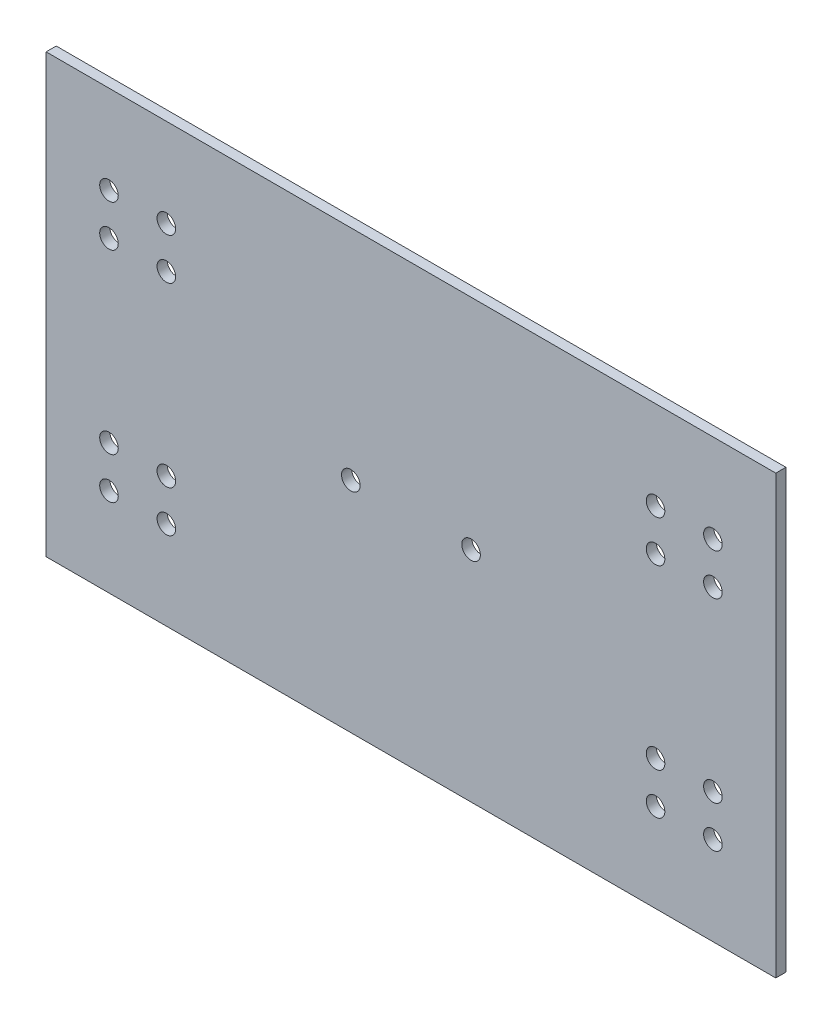
SolidWorks part; units mm, degrees
ref_plane "Alzado" through (0, 0, 0) normal (0, 0, 1) x (1, 0, 0)
ref_plane "Planta" through (0, 0, 0) normal (0, 1, 0) x (1, 0, 0)
ref_plane "Vista lateral" through (0, 0, 0) normal (1, 0, 0) x (0, 0, -1)
sketch "Sketch1" plane through (0, 0, 0) normal (0, 0, 1) x (1, 0, 0)
  line L0 (267, 160) -> (267, 0)
  line L1 (267, 160) -> (0, 160)
  line L2 (267, 0) -> (0, 0)
  line L3 (0, 160) -> (0, 0)
  line L4 (23, 51) -> (-40.3044, 51) construction
  line L5 (23, 29) -> (-41.338, 29) construction
  line L6 (47.4, 47.6) -> (47.4, 14.1246) construction
  line L7 (19.6, 47.6) -> (19.6, 13.494) construction
  line L8 (23, 47.6) -> (44, 32.4) construction
  line L9 (23, 32.4) -> (44, 47.6) construction
  line L10 (133.5, 40) -> (133.5, 23.6262) construction
  line L11 (267, 80) -> (183.2601, 80) construction
  line L12 (183.2601, 60) -> (104.6684, 60) construction
  circle A0 centre (6, 154) radius 3.4
  circle A1 centre (6, 6) radius 3.4
  circle A2 centre (261, 154) radius 3.4
  circle A3 centre (261, 6) radius 3.4
  circle A4 centre (111.5, 40) radius 3.4
  circle A5 centre (155.5, 40) radius 3.4
  circle A6 centre (23, 47.6) radius 3.4
  circle A7 centre (44, 47.6) radius 3.4
  circle A8 centre (23, 32.4) radius 3.4
  circle A9 centre (44, 32.4) radius 3.4
  circle A10 centre (223, 32.4) radius 3.4
  circle A11 centre (223, 47.6) radius 3.4
  circle A12 centre (244, 47.6) radius 3.4
  circle A13 centre (244, 32.4) radius 3.4
  circle A14 centre (23, 127.6) radius 3.4
  circle A15 centre (23, 112.4) radius 3.4
  circle A16 centre (44, 112.4) radius 3.4
  circle A17 centre (44, 127.6) radius 3.4
  circle A18 centre (223, 112.4) radius 3.4
  circle A19 centre (223, 127.6) radius 3.4
  circle A20 centre (244, 127.6) radius 3.4
  circle A21 centre (244, 112.4) radius 3.4
  circle A22 centre (111.5, 80) radius 3.4
  circle A23 centre (155.5, 80) radius 3.4
  point P32 (33.5, 40)
  point P35 (133.5, 40)
  dimension "D1" = 6.8
  dimension "D2" = 22
  dimension "D3" = 27.8
  dimension "D4" = 44
  dimension "D5" = 22
  dimension "D6" = 100
  dimension "D7" = 160
  dimension "D8" = 6
  dimension "D9" = 6
  dimension "D10" = 6
  dimension "D11" = 6
  dimension "D12" = 6
  dimension "D13" = 6
  dimension "D14" = 6
  dimension "D15" = 6
  dimension "D16" = 17
  dimension "D17" = 17
  dimension "D18" = 40
  dimension "D19" = 100
  dimension "D20" = 20
extrude "Boss-Extrude1" add sketch "Sketch1" along normal blind 3.7 contours L1 L3 L2 L0 A22 A21 A20 A19 A18 A16 A14 A12 A10 A9 A8 A7 A6 A5 A4 A3 A2 A1 A0 A11 A13 A15 A17
